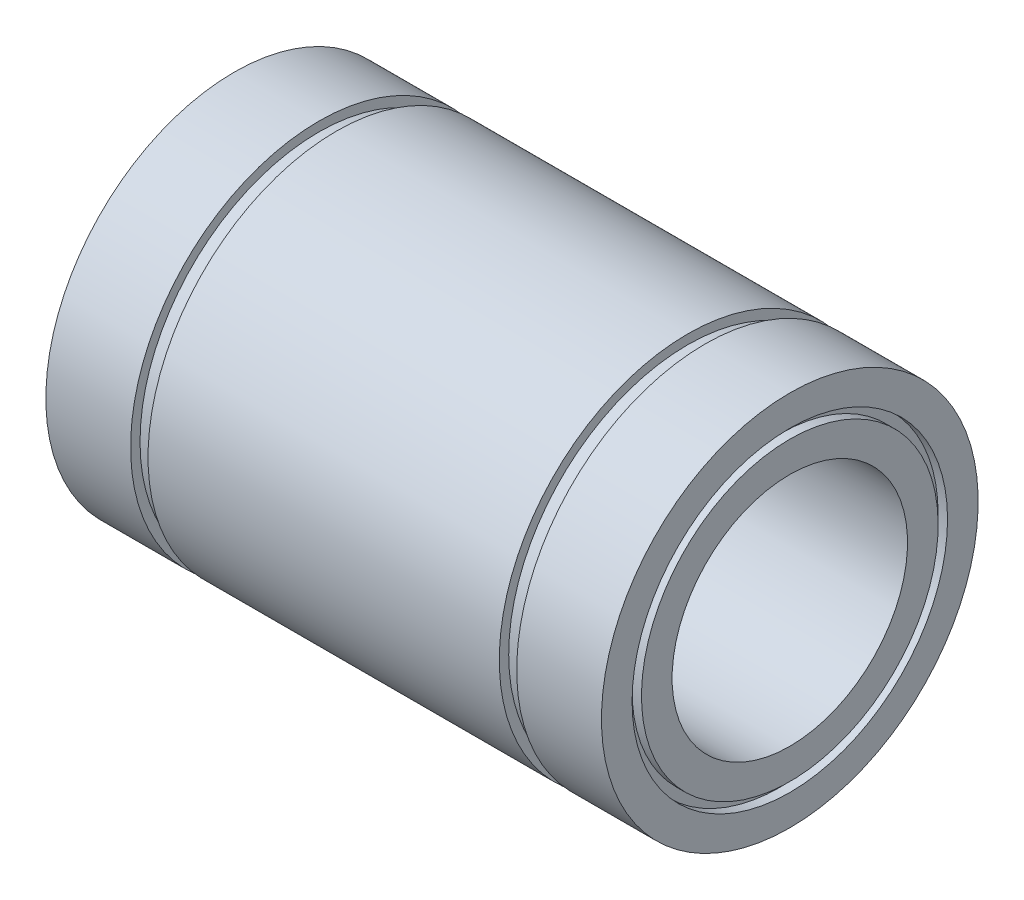
SolidWorks part; units mm, degrees
material "Ст3сп ГОСТ 535-2005"
ref_plane "Plano frontal" through (0, 0, 0) normal (0, 0, 1) x (1, 0, 0)
ref_plane "Plano superior" through (0, 0, 0) normal (0, 1, 0) x (1, 0, 0)
ref_plane "Plano direito" through (0, 0, 0) normal (1, 0, 0) x (0, 0, -1)
sketch "Esboço1" plane through (0, 0, 0) normal (0, 0, 1) x (1, 0, 0)
  line L0 (-29.5, 20) -> (-20.5, 20)
  line L1 (-20.5, 20) -> (-20.5, 19)
  line L2 (-20.5, 19) -> (-18.65, 19)
  line L3 (-18.65, 19) -> (-18.65, 20)
  line L4 (-18.65, 20) -> (18.65, 20)
  line L5 (18.65, 20) -> (18.65, 19)
  line L6 (18.65, 19) -> (20.5, 19)
  line L7 (20.5, 19) -> (20.5, 20)
  line L8 (20.5, 20) -> (29.5, 20)
  line L9 (29.5, 20) -> (29.5, 16.75)
  line L10 (29.5, 12.5) -> (-29.5, 12.5)
  line L11 (-29.5, 12.5) -> (-29.5, 15.75)
  line L12 (0, 12.5) -> (0, 0) construction
  line L13 (0, 0) -> (-86.5, 0) construction
  line L14 (-29.5, 16.75) -> (-29.5, 20)
  line L15 (-29.5, 16.75) -> (-28.5, 16.75)
  line L16 (29.5, 15.75) -> (29.5, 12.5)
  line L17 (-28.5, 16.75) -> (-28.5, 15.75)
  line L18 (-28.5, 15.75) -> (-29.5, 15.75)
  line L19 (29.5, 16.75) -> (28.5, 16.75)
  line L21 (29.5, 15.75) -> (28.5, 15.75)
  line L22 (28.5, 16.75) -> (28.5, 15.75)
  dimension "D1" = 59
  dimension "D2" = 41
  dimension "D3" = 1.85
  dimension "D4" = 25
  dimension "D5" = 40
  dimension "D6" = 38
  dimension "D7" = 1
  dimension "D8" = 1
  dimension "D9" = 1
  dimension "D10" = 1
revolve "Revolução1" add sketch "Esboço1" angle 360 about L13
